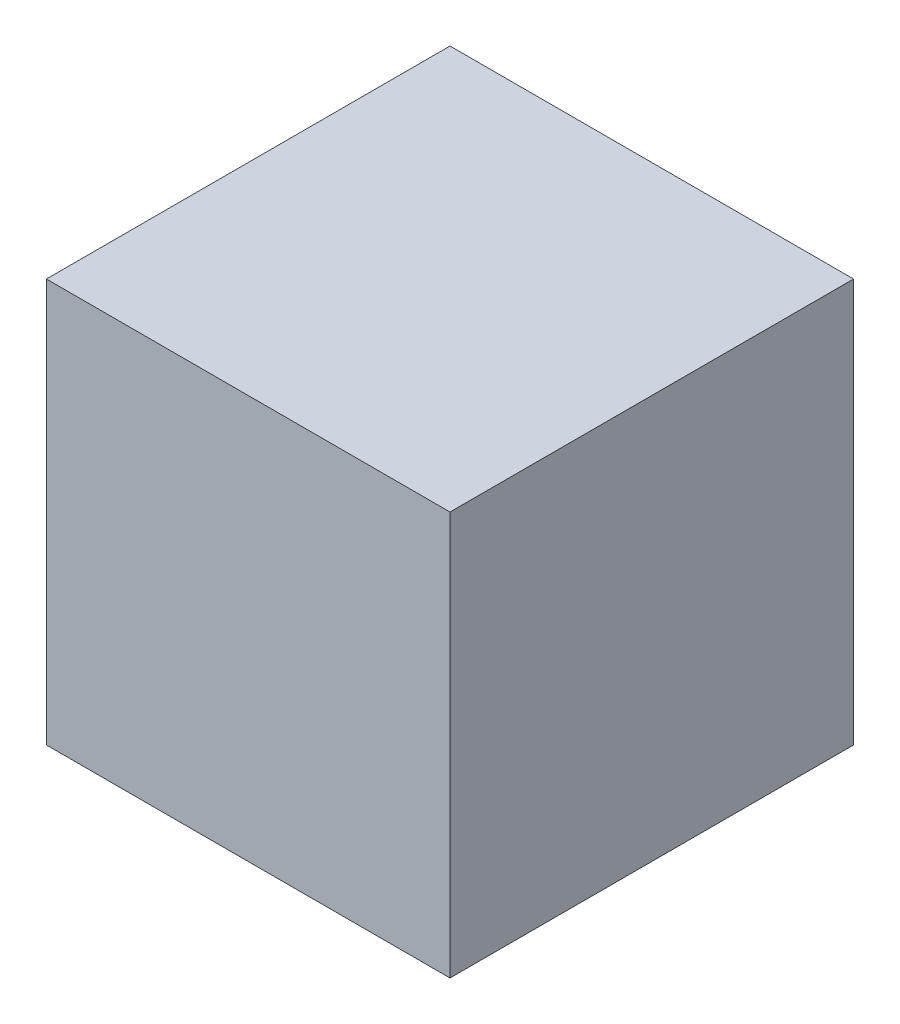
SolidWorks part; units mm, degrees
ref_plane "Front Plane" through (0, 0, 0) normal (0, 0, 1) x (1, 0, 0)
ref_plane "Top Plane" through (0, 0, 0) normal (0, 1, 0) x (1, 0, 0)
ref_plane "Right Plane" through (0, 0, 0) normal (1, 0, 0) x (0, 0, -1)
sketch "Sketch1" plane through (0, 0, 0) normal (0, 0, 1) x (1, 0, 0)
  line L1 (-28.5, -28.5) -> (28.5, -28.5)
  line L2 (-28.5, -28.5) -> (-28.5, 28.5)
  line L3 (-28.5, 28.5) -> (28.5, 28.5)
  line L4 (28.5, -28.5) -> (28.5, 28.5)
  line L5 (-28.5, -28.5) -> (28.5, 28.5) construction
  line L6 (-28.5, 28.5) -> (28.5, -28.5) construction
  point P0 (0, 0)
  dimension "D1" = 57
extrude "Boss-Extrude1" add sketch "Sketch1" along normal blind 57
